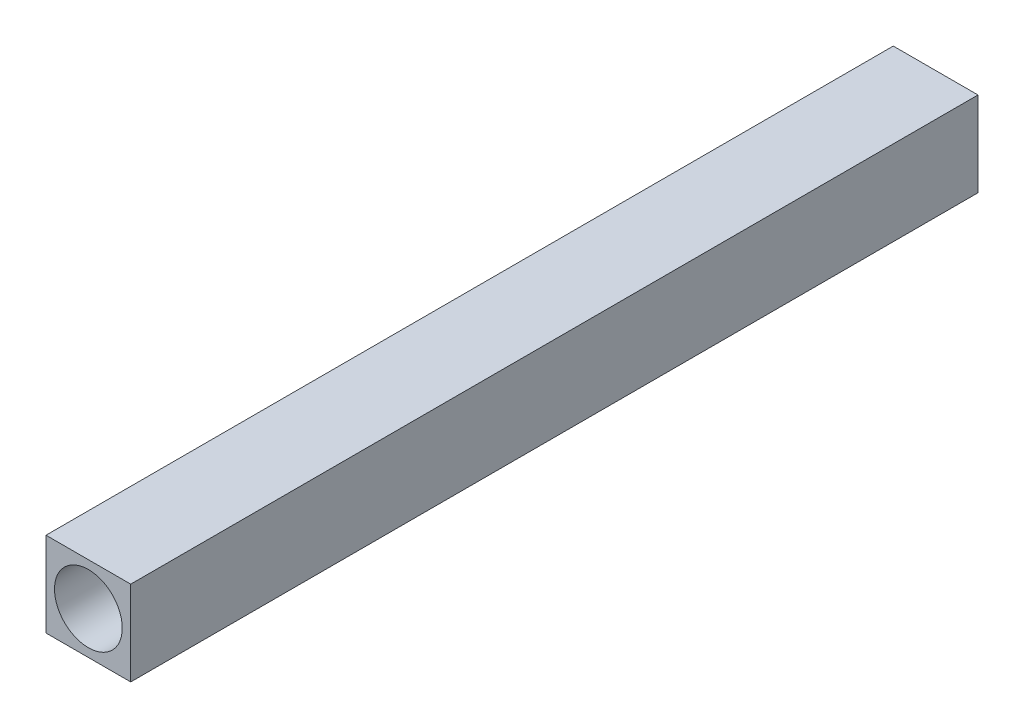
SolidWorks part; units mm, degrees
ref_plane "Front" through (0, 0, 0) normal (0, 0, 1) x (1, 0, 0)
ref_plane "Top" through (0, 0, 0) normal (0, 1, 0) x (1, 0, 0)
ref_plane "Right" through (0, 0, 0) normal (1, 0, 0) x (0, 0, -1)
sketch "草图1" plane through (0, 0, 0) normal (0, 0, 1) x (1, 0, 0)
  line L1 (-5, 5) -> (5, 5)
  line L2 (-5, 5) -> (-5, -5)
  line L3 (-5, -5) -> (5, -5)
  line L4 (5, 5) -> (5, -5)
  dimension "D1" = 10
  dimension "D2" = 10
  dimension "D3" = 5
  dimension "D4" = 5
extrude "凸台-拉伸1" add sketch "草图1" along normal blind 100
sketch "草图2" plane through (0, 0, 100) normal (0, 0, 1) x (1, 0, 0)
  circle A0 centre (0, 0) radius 4
extrude "切除-拉伸1" cut sketch "草图2" against normal blind 90
